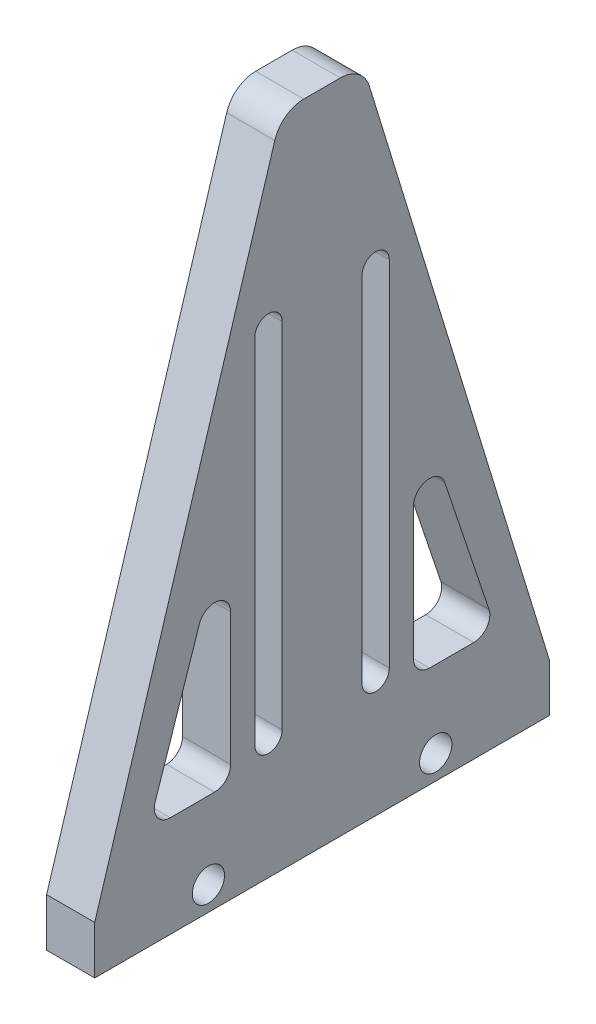
SolidWorks part; units mm, degrees
material "6061-T6 (SS)"
ref_plane "Front Plane" through (0, 0, 0) normal (0, 0, 1) x (1, 0, 0)
ref_plane "Top Plane" through (0, 0, 0) normal (0, 1, 0) x (1, 0, 0)
ref_plane "Right Plane" through (0, 0, 0) normal (1, 0, 0) x (0, 0, -1)
sketch "Sketch1" plane through (0, 0, 0) normal (1, 0, 0) x (0, 0, -1)
  line L0 (-22.5, 0) -> (22.5, 0)
  line L1 (-22.5, 0) -> (-22.5, 4.763)
  line L2 (22.5, 0) -> (22.5, 4.763)
  line L3 (0, 0) -> (0, 78.0018) construction
  line L4 (-4.6779, 62.8796) -> (-22.5, 4.763)
  line L5 (22.5, 4.763) -> (4.6779, 62.8796)
  line L6 (-5.305, 47) -> (5.305, 47) construction
  line L7 (-5.305, 12) -> (5.305, 12) construction
  line L8 (-5.305, 47) -> (-5.305, 12) construction
  line L9 (-3.955, 47) -> (-3.955, 12)
  line L10 (-6.655, 47) -> (-6.655, 12)
  line L11 (5.305, 47) -> (5.305, 12) construction
  line L12 (6.655, 47) -> (6.655, 12)
  line L13 (3.955, 47) -> (3.955, 12)
  line L14 (-1.8097, 65) -> (1.8097, 65)
  line L15 (12.1384, 25.1646) -> (16.5221, 12.0922)
  line L16 (-9.0457, 24.6598) -> (-9.0457, 11.5875)
  line L17 (-15.017, 10) -> (-10.6332, 10)
  line L18 (-12.1384, 25.1646) -> (-16.5221, 12.0922)
  line L19 (15.017, 10) -> (10.6332, 10)
  line L20 (9.0457, 24.6598) -> (9.0457, 11.5875)
  line L21 (0, 39.0009) -> (5.3033, 44.3042) construction
  line L22 (0, 39.0009) -> (-5.3033, 33.6976) construction
  line L23 (-17.2237, 10) -> (-7.537, 39.0009) construction
  arc A0 (-9.0457, 24.6598) -> (-12.1384, 25.1646) centre (-10.6332, 24.6598) ccw
  arc A1 (-10.6332, 10) -> (-9.0457, 11.5875) centre (-10.6332, 11.5875) ccw
  arc A2 (-3.955, 47) -> (-6.655, 47) centre (-5.305, 47) ccw
  arc A3 (-6.655, 12) -> (-3.955, 12) centre (-5.305, 12) ccw
  arc A4 (6.655, 47) -> (3.955, 47) centre (5.305, 47) ccw
  arc A5 (3.955, 12) -> (6.655, 12) centre (5.305, 12) ccw
  arc A6 (1.8097, 65) -> (4.6779, 62.8796) centre (1.8097, 62) cw
  arc A7 (-1.8097, 65) -> (-4.6779, 62.8796) centre (-1.8097, 62) ccw
  arc A8 (-15.017, 10) -> (-16.5221, 12.0922) centre (-15.017, 11.5875) cw
  arc A9 (15.017, 10) -> (16.5221, 12.0922) centre (15.017, 11.5875) ccw
  arc A10 (10.6332, 10) -> (9.0457, 11.5875) centre (10.6332, 11.5875) cw
  arc A11 (9.0457, 24.6598) -> (12.1384, 25.1646) centre (10.6332, 24.6598) cw
  point P3 (0, 0)
  point P10 (0, 47)
  point P11 (0, 60)
  point P12 (-16.4694, 12.2383)
  point P15 (0, 12)
  point P16 (22.5, 2.3815)
  point P17 (-5.305, 29.5)
  point P22 (5.305, 29.5)
  point P27 (4.0276, 65)
  point P28 (-4.0276, 65)
  point P33 (-9.0457, 34.3868)
  point P37 (4.0276, 65)
  point P40 (-4.0276, 65)
  point P41 (-17.2237, 10)
  point P42 (-12.1325, 25.1069)
  point P43 (-9.0457, 10)
  point P47 (-22.5, 2.3815)
  point P49 (-11.25, 5)
  point P51 (11.25, 5)
  point P55 (-9.0457, 34.3868)
  point P58 (-9.0457, 10)
  point P61 (-17.2237, 10)
  point P65 (17.2237, 10)
  point P66 (9.0457, 10)
  point P67 (9.0457, 34.3868)
  point P68 (12.1325, 25.1069)
  point P69 (16.4694, 12.2383)
  point P70 (0, 39.0009)
  dimension "D1" = 3
  dimension "D2" = 1.5875
  dimension "D3" = 1.5875
  dimension "D4" = 4.763
  dimension "D5" = 45
  dimension "D6" = 65
extrude "Boss-Extrude1" add sketch "Sketch1" along normal mid plane 4.763
hole_wizard "M3 Clearance Hole1" positions "Sketch3" profile "Sketch2" hole size "M3" standard "ANSI Metric" end condition through all
sketch "Sketch3" plane through (2.3815, 0, 0) normal (1, 0, 0) x (0, 0, -1)
  line L0 (-22.5, 2.3815) -> (22.5, 2.3815) construction
  line L1 (-22.5, 4.763) -> (-22.5, 0) construction
  line L2 (22.5, 0) -> (22.5, 4.763) construction
  point P0 (-11.25, 2.3815)
  point P2 (11.25, 2.3815)
  dimension "D1" = 11.25
  dimension "D2" = 11.25
sketch "Sketch2" plane through (2.3815, 2.3815, 11.25) normal (0, 1, 0) x (0, 0, -1)
  line L0 (0, 0) -> (0, 4.763)
  line L1 (0, 4.763) -> (1.6, 4.763)
  line L2 (1.6, 4.763) -> (1.6, 0)
  line L5 (1.6, 0) -> (0, 0)
  line L11 (0, -6.35) -> (0, 107.95) construction
  dimension "Thru Hole Dia." = 3.2
  dimension "Thru Hole Depth" = 4.763
